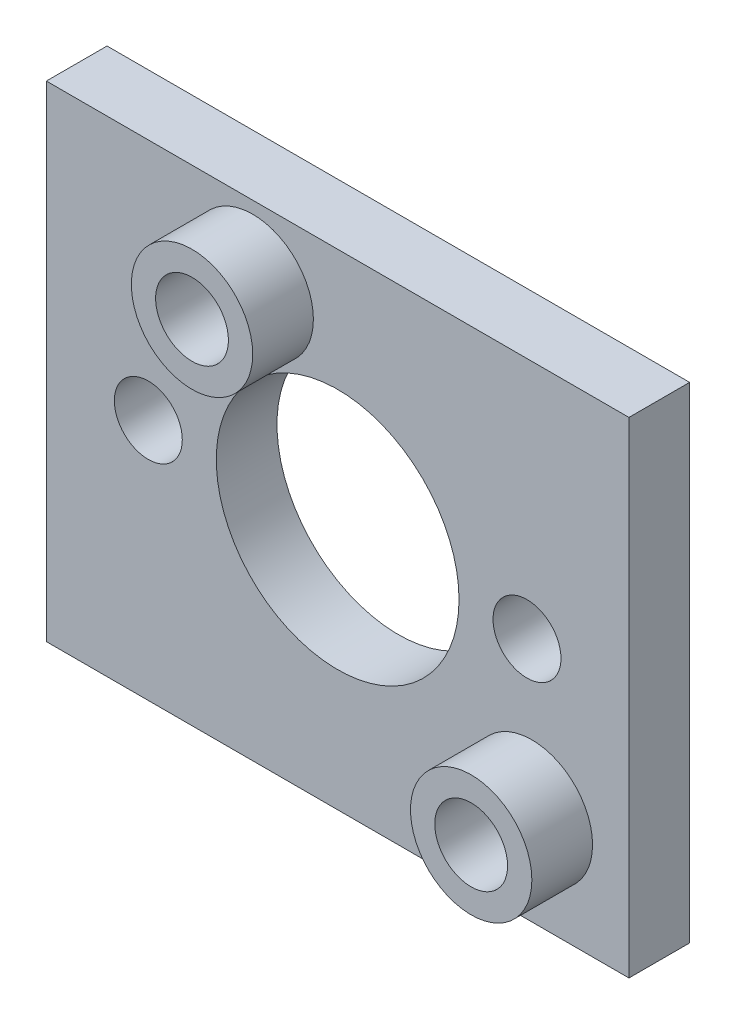
SolidWorks part; units mm, degrees
material "Copper"
ref_plane "Front Plane" through (0, 0, 0) normal (0, 0, 1) x (1, 0, 0)
ref_plane "Top Plane" through (0, 0, 0) normal (0, 1, 0) x (1, 0, 0)
ref_plane "Right Plane" through (0, 0, 0) normal (1, 0, 0) x (0, 0, -1)
sketch "Sketch1" plane through (0, 0, 0) normal (0, 0, 1) x (1, 0, 0)
  line L1 (15.24, -12.7) -> (-15.24, -12.7)
  line L2 (15.24, -12.7) -> (15.24, 12.7)
  line L3 (15.24, 12.7) -> (-15.24, 12.7)
  line L4 (-15.24, -12.7) -> (-15.24, 12.7)
  line L5 (15.24, -12.7) -> (-15.24, 12.7) construction
  line L6 (15.24, 12.7) -> (-15.24, -12.7) construction
  circle A0 centre (0, 0) radius 6.35
  circle A1 centre (-9.906, 0) radius 1.778
  circle A2 centre (9.906, 0) radius 1.778
  point P0 (0, 0)
  point P12 (0, 0)
  dimension "D3" = 12.7
  dimension "D4" = 3.556
  dimension "D5" = 3.556
  dimension "D1" = 25.4
  dimension "D2" = 30.48
  dimension "D6" = 9.906
  dimension "D7" = 9.906
extrude "Boss-Extrude1" add sketch "Sketch1" along normal blind 3.175
sketch "Sketch2" plane through (0, 0, 3.175) normal (0, 0, 1) x (1, 0, 0)
  line L0 (15.24, -12.7) -> (15.24, 12.7) construction
  line L1 (-15.24, -12.7) -> (15.24, -12.7) construction
  circle A0 centre (10.16, -7.62) radius 1.905
  circle A1 centre (-4.445, 8.89) radius 1.905
  circle A2 centre (-4.445, 8.89) radius 3.175
  circle A3 centre (10.16, -7.62) radius 3.175
  dimension "D5" = 3.81
  dimension "D6" = 6.35
  dimension "D7" = 3.81
  dimension "D8" = 6.35
  dimension "D1" = 5.08
  dimension "D2" = 5.08
  dimension "D3" = 16.51
  dimension "D4" = 14.605
extrude "Boss-Extrude2" add sketch "Sketch2" along normal blind 3.175
